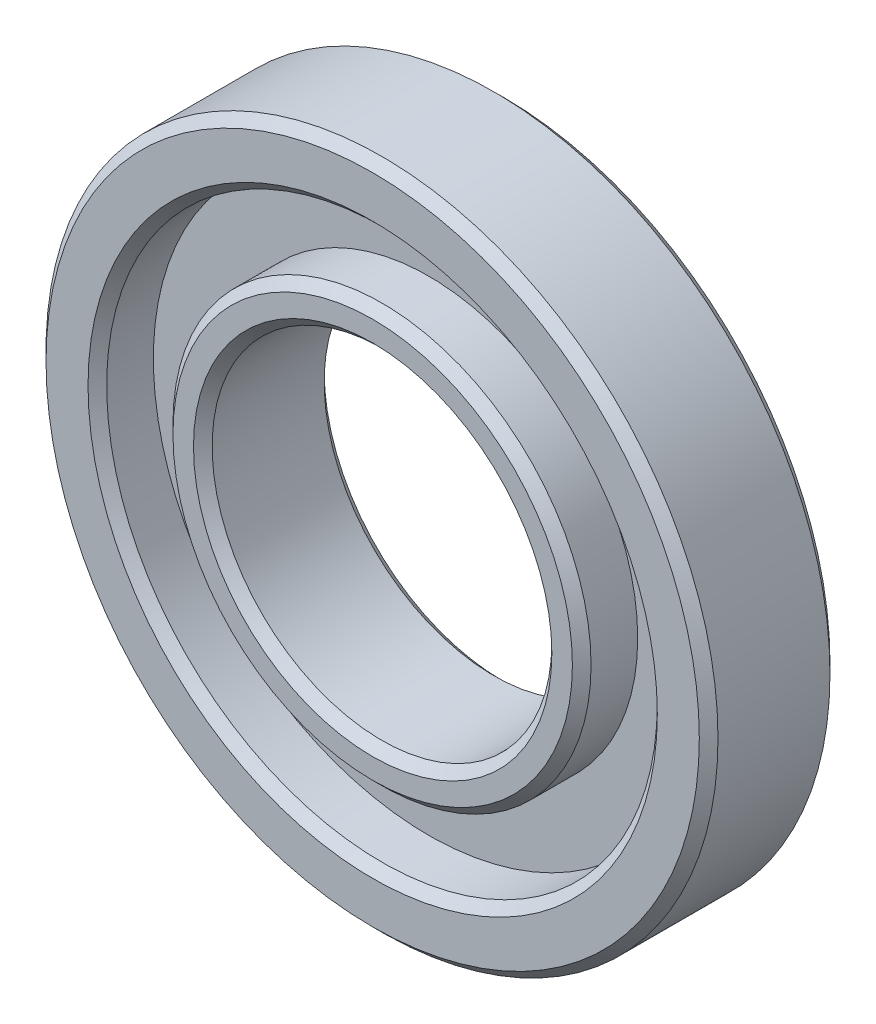
SolidWorks part; units mm, degrees
ref_plane "Alzado" through (0, 0, 0) normal (0, 0, 1) x (1, 0, 0)
ref_plane "Planta" through (0, 0, 0) normal (0, 1, 0) x (1, 0, 0)
ref_plane "Vista lateral" through (0, 0, 0) normal (1, 0, 0) x (0, 0, -1)
sketch "Croquis1" plane through (0, 0, 0) normal (0, 0, 1) x (1, 0, 0)
  circle A0 centre (0, 0) radius 18
  circle A1 centre (0, 0) radius 9.1
  dimension "D1" = 36
  dimension "D2" = 18.2
extrude "Saliente-Extruir1" add sketch "Croquis1" along normal blind 7
sketch "Croquis2" plane through (0, 0, 7) normal (0, 0, 1) x (1, 0, 0)
  circle A0 centre (0, 0) radius 14.75
  circle A1 centre (0, 0) radius 11.2
  dimension "D1" = 29.5
  dimension "D2" = 22.4
extrude "Cortar-Extruir1" cut sketch "Croquis2" against normal blind 3
chamfer "Chaflán1" distance 0.5 angle 45 6 edges at (9.1, 0, 0) (18, 0, 0) (9.1, 0, 7) (11.2, 0, 7) (14.75, 0, 7) (18, 0, 7)
